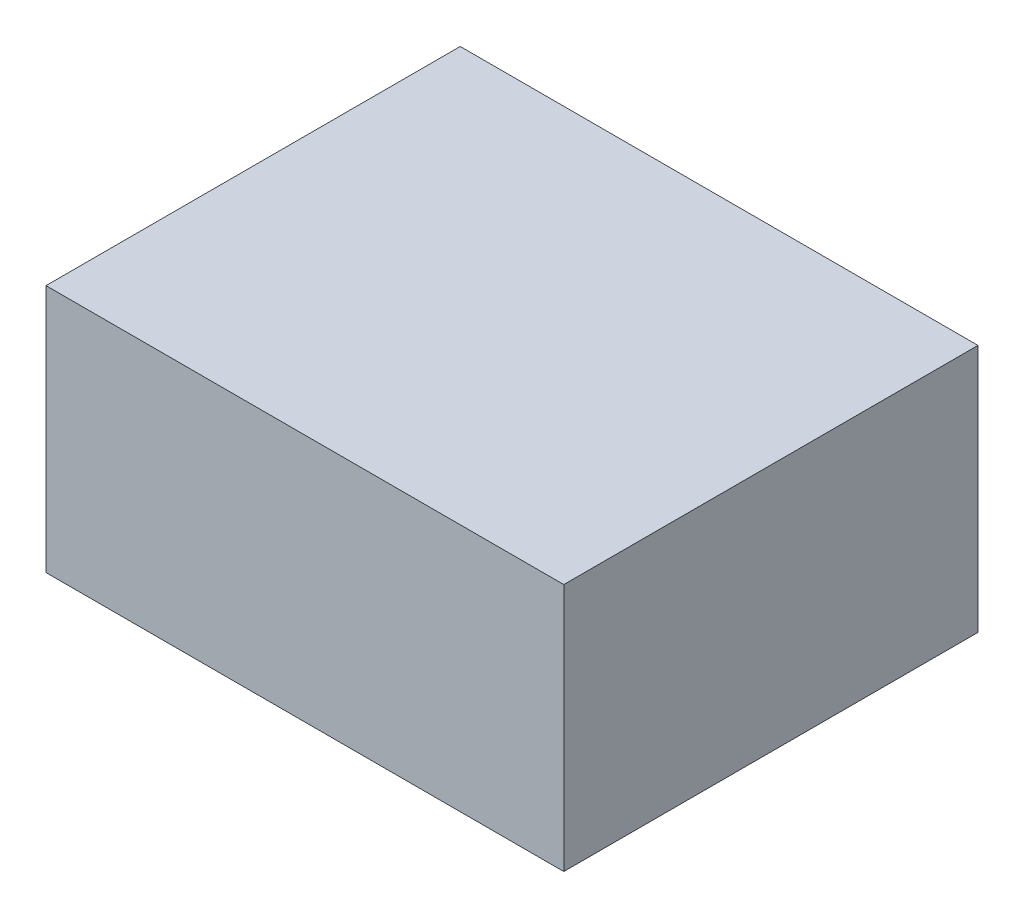
SolidWorks part; units mm, degrees
ref_plane "Front Plane" through (0, 0, 0) normal (0, 0, 1) x (1, 0, 0)
ref_plane "Top Plane" through (0, 0, 0) normal (0, 1, 0) x (1, 0, 0)
ref_plane "Right Plane" through (0, 0, 0) normal (1, 0, 0) x (0, 0, -1)
sketch "Sketch1" plane through (0, 0, 0) normal (0, 0, 1) x (1, 0, 0)
  line L0 (-162.0402, 0) -> (161.9956, 0) construction
  line L1 (0, 104.4441) -> (0, -68.4928) construction
  line L2 (-100, 104.4441) -> (-100, -97.3979) construction
  line L3 (100, 104.4441) -> (100, -97.3979) construction
  line L4 (-162.0402, -68.4928) -> (162.0402, -68.4928) construction
  line L5 (-162.0402, 70) -> (161.9956, 70) construction
  line L7 (-50, 30) -> (75, 30)
  line L8 (-50, 30) -> (-50, -30)
  line L9 (-50, -30) -> (75, -30)
  line L10 (75, 30) -> (75, -30)
  point P17 (-0.0223, -68.4928)
  dimension "D1" = 100
  dimension "D2" = 70
  dimension "D3" = 100
  dimension "D4" = 40
  dimension "D5" = 30
  dimension "D6" = 25
  dimension "D7" = 50
extrude "Boss-Extrude1" add sketch "Sketch1" along normal blind 100
